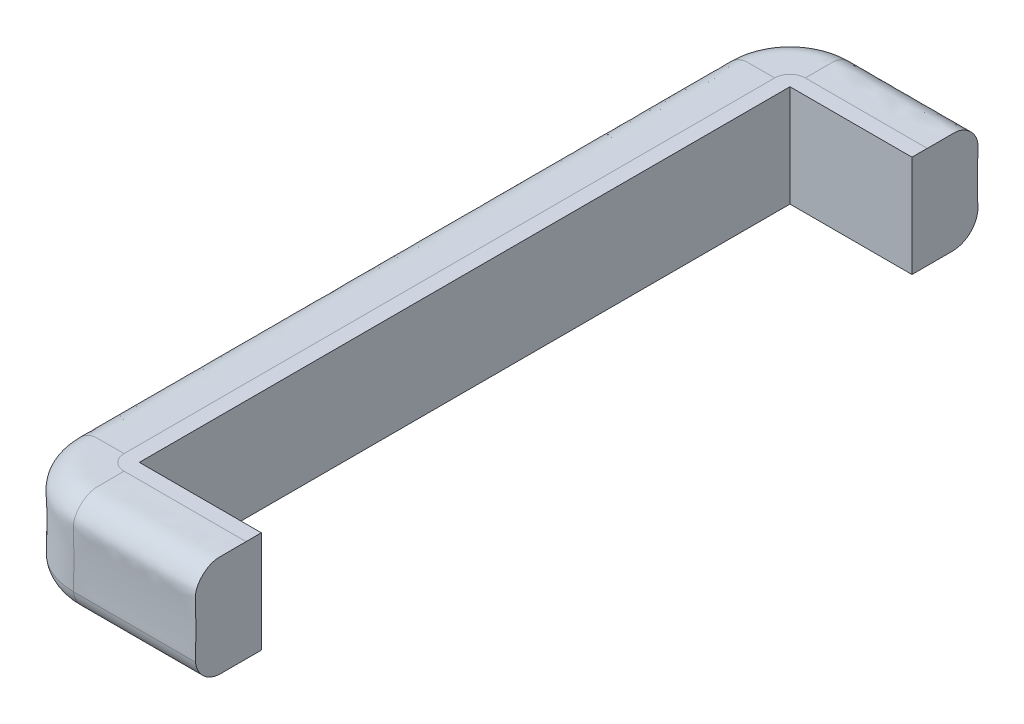
SolidWorks part; units mm, degrees
material "Polyurethane Foam Flexible"
ref_plane "Front Plane" through (0, 0, 0) normal (0, 0, 1) x (1, 0, 0)
ref_plane "Top Plane" through (0, 0, 0) normal (0, 1, 0) x (1, 0, 0)
ref_plane "Right Plane" through (0, 0, 0) normal (1, 0, 0) x (0, 0, -1)
sketch "Sketch1" plane through (0, 0, 0) normal (0, 0, 1) x (1, 0, 0)
  line L0 (-42.938, 0) -> (-64.5194, 0) construction
  line L1 (0, 0) -> (-19.05, 0)
  line L2 (0, 0) -> (0, 127)
  line L3 (0, 127) -> (-19.05, 127)
  line L4 (-19.05, 0) -> (-19.05, 127)
  line L5 (-82.4248, 61.7932) -> (-82.5169, 106.4686) construction
  line L6 (-82.3392, 20.316) -> (-82.421, 59.9925) construction
  line L7 (-25.1859, 127) -> (-9.5237, 127) construction
  line L8 (-59.4349, 127) -> (-40.1051, 127) construction
  circle A0 centre (-50.8, 95.25) radius 31.75
  circle A1 centre (-50.8, 31.75) radius 31.75
  spline S0 degree 3 poles (-19.05, 127) (-25.8552, 127) (-41.6978, 126.7791) (-65.8751, 127.402) (-83.5455, 110.8616) (-81.483, 80.6655) (-81.4888, 44.9734) (-83.2203, 14.9745) (-68.5084, -0.3764) (-39.2535, 0.2129) (-30.1777, 0.1792) (-19.05, 0) knots 0 0 0 0 0.126865 0.164018 0.34847 0.398266 0.612182 0.660911 0.836821 0.872929 1 1 1 1
  dimension "D1" = 19.05
  dimension "D2" = 63.5
extrude "Boss-Extrude1" add sketch "Sketch1" along normal blind 812.8 contours A0 S0 A1 | A1 L4 A0 | L4 S0 A0 | A0 S0 | A1 S0 | A0 S0 | A1 S0 L4 | L4 L1 L2 L3
sketch "Sketch2" plane through (0, 0, 812.8) normal (0, 0, 1) x (1, 0, 0)
  line L3 (-19.05, 0) -> (0, 0)
  line L4 (0, 0) -> (0, 127)
  line L5 (0, 127) -> (-19.05, 127)
  line L6 (-19.05, 0) -> (0, 0)
  line L7 (0, 0) -> (0, 127)
  line L8 (0, 127) -> (-19.05, 127)
  arc A1 (-82.3555, 28.2414) -> (-50.8, 0) centre (-50.8, 31.75) ccw
  arc A2 (-82.3555, 28.2414) -> (-50.8, 0) centre (-50.8, 31.75) ccw
  spline S2 degree 3 poles (-3014.4787, -37.5012) (256.1734, 142.9451) (16.9783, 125.2675) (-65.8751, 127.402) (-83.5455, 110.8616) (-81.483, 80.6655) (-81.5023, -38.9836) (-96.4116, 20.7178) (2684.799, -1129.6695) knots -0.845708 -0.845708 -0.845708 -0.845708 0.126865 0.164018 0.34847 0.398266 0.612182 1.39585 1.39585 1.39585 1.39585 only from (-19.05, 127) to (-82.3555, 28.2414)
  spline S3 degree 3 poles (1998.3135, 2187.1841) (-227.7169, -6.5891) (99.7338, 8.0795) (-73.8503, -9.0254) (2980.7785, -12.4885) knots 0.228756 0.228756 0.228756 0.228756 0.872929 1.861828 1.861828 1.861828 1.861828 only from (-50.8, 0) to (-19.05, 0)
  spline S4 degree 3 poles (-19.05, 127) (-25.8552, 127) (-41.6978, 126.7791) (-65.8751, 127.402) (-83.5455, 110.8616) (-81.483, 80.6655) (-81.4884, 47.4854) (-82.3594, 30.1001) (-82.3555, 28.2414) knots 0 0 0 0 0.126865 0.164018 0.34847 0.398266 0.612182 0.638922 0.638922 0.638922 0.638922
  spline S5 degree 3 poles (-50.8, 0) (-49.6284, 0) (-38.0305, 0.2084) (-30.1777, 0.1792) (-19.05, 0) knots 0.85881 0.85881 0.85881 0.85881 0.872929 1 1 1 1
  dimension "D1" = 0
revolve "Revolve1" add sketch "Sketch2" angle 90 about L7
sketch "Sketch4" plane through (0, 0, 0) normal (0, 0, -1) x (-1, 0, 0)
  line L3 (19.05, 127) -> (0, 127)
  line L4 (0, 127) -> (0, 0)
  line L5 (0, 0) -> (19.05, 0)
  line L6 (19.05, 127) -> (0, 127)
  line L7 (0, 127) -> (0, 0)
  line L8 (0, 0) -> (19.05, 0)
  arc A1 (50.8, 0) -> (82.3555, 28.2414) centre (50.8, 31.75) ccw
  arc A2 (50.8, 0) -> (82.3555, 28.2414) centre (50.8, 31.75) ccw
  spline S2 degree 3 poles (-2684.8304, -1129.6825) (96.4117, 20.7181) (81.5023, -38.9839) (81.483, 80.6655) (83.5455, 110.8616) (65.8751, 127.402) (-16.9777, 125.2675) (-256.1693, 142.9448) (3014.3918, -37.4964) knots -0.756931 -0.756931 -0.756931 -0.756931 0.026739 0.240655 0.290451 0.474904 0.512057 1.484621 1.484621 1.484621 1.484621 only from (82.3555, 28.2414) to (19.05, 127)
  spline S3 degree 3 poles (-2980.8609, -12.4886) (73.8522, -9.0256) (-99.7352, 8.0795) (227.7155, -6.5891) (-1998.2775, 2187.1486) knots -0.003027 -0.003027 -0.003027 -0.003027 0.985881 1.630051 1.630051 1.630051 1.630051 only from (19.05, 0) to (50.8, 0)
  spline S4 degree 3 poles (82.3555, 28.2414) (82.3594, 30.1001) (81.4884, 47.4854) (81.483, 80.6655) (83.5455, 110.8616) (65.8751, 127.402) (41.6978, 126.7791) (25.8552, 127) (19.05, 127) knots 0 0 0 0 0.026739 0.240655 0.290451 0.474904 0.512057 0.638922 0.638922 0.638922 0.638922
  spline S5 degree 3 poles (19.05, 0) (30.1777, 0.1792) (38.0305, 0.2084) (49.6284, 0) (50.8, 0) knots 0.85881 0.85881 0.85881 0.85881 0.985881 1 1 1 1
  dimension "D1" = 0
revolve "Revolve2" add sketch "Sketch4" angle 90 about L7
sketch "Sketch5" plane through (0, 0, 0) normal (1, 0, 0) x (0, 0, -1)
  line L0 (-812.8, 127) -> (-812.8, 0)
  line L1 (-812.8, 127) -> (-812.8, 28.2414) construction
  line L2 (-831.85, 0) -> (19.05, 0)
  line L3 (19.05, 127) -> (-831.85, 127)
  line L4 (-831.85, 0) -> (19.05, 0)
  line L5 (19.05, 127) -> (-831.85, 127)
  line L6 (0, 127) -> (0, 0)
  arc A2 (50.8, 0) -> (82.3555, 28.2414) centre (50.8, 31.75) ccw
  arc A3 (-895.1555, 28.2414) -> (-863.6, 0) centre (-863.6, 31.75) ccw
  arc A4 (50.8, 0) -> (82.3555, 28.2414) centre (50.8, 31.75) ccw
  arc A5 (-895.1555, 28.2414) -> (-863.6, 0) centre (-863.6, 31.75) ccw
  spline S4 degree 3 poles (-2980.8609, -12.4886) (73.8522, -9.0256) (-99.7352, 8.0795) (227.7155, -6.5891) (-1998.2775, 2187.1486) knots -0.003027 -0.003027 -0.003027 -0.003027 0.985881 1.630051 1.630051 1.630051 1.630051 only from (19.05, 0) to (50.8, 0)
  spline S5 degree 3 poles (-2684.8304, -1129.6825) (96.4117, 20.7181) (81.5023, -38.9839) (81.483, 80.6655) (83.5455, 110.8616) (65.8751, 127.402) (-16.9777, 125.2675) (-256.1693, 142.9448) (3014.3918, -37.4964) knots -0.756931 -0.756931 -0.756931 -0.756931 0.026739 0.240655 0.290451 0.474904 0.512057 1.484621 1.484621 1.484621 1.484621 only from (82.3555, 28.2414) to (19.05, 127)
  spline S6 degree 3 poles (-3827.2787, -37.5012) (-556.6266, 142.9451) (-795.8217, 125.2675) (-878.6751, 127.402) (-896.3455, 110.8616) (-894.283, 80.6655) (-894.3023, -38.9836) (-909.2116, 20.7178) (1871.999, -1129.6695) knots -0.845708 -0.845708 -0.845708 -0.845708 0.126865 0.164018 0.34847 0.398266 0.612182 1.39585 1.39585 1.39585 1.39585 only from (-831.85, 127) to (-895.1555, 28.2414)
  spline S7 degree 3 poles (1185.5135, 2187.1841) (-1040.5169, -6.5891) (-713.0662, 8.0795) (-886.6503, -9.0254) (2167.9785, -12.4885) knots 0.228756 0.228756 0.228756 0.228756 0.872929 1.861828 1.861828 1.861828 1.861828 only from (-863.6, 0) to (-831.85, 0)
  spline S8 degree 3 poles (19.05, 0) (30.1777, 0.1792) (38.0305, 0.2084) (49.6284, 0) (50.8, 0) knots 0.85881 0.85881 0.85881 0.85881 0.985881 1 1 1 1
  spline S9 degree 3 poles (82.3555, 28.2414) (82.3594, 30.1001) (81.4884, 47.4854) (81.483, 80.6655) (83.5455, 110.8616) (65.8751, 127.402) (41.6978, 126.7791) (25.8552, 127) (19.05, 127) knots 0 0 0 0 0.026739 0.240655 0.290451 0.474904 0.512057 0.638922 0.638922 0.638922 0.638922
  spline S10 degree 3 poles (-831.85, 127) (-838.6552, 127) (-854.4978, 126.7791) (-878.6751, 127.402) (-896.3455, 110.8616) (-894.283, 80.6655) (-894.2884, 47.4854) (-895.1594, 30.1001) (-895.1555, 28.2414) knots 0 0 0 0 0.126865 0.164018 0.34847 0.398266 0.612182 0.638922 0.638922 0.638922 0.638922
  spline S11 degree 3 poles (-863.6, 0) (-862.4284, 0) (-850.8305, 0.2084) (-842.9777, 0.1792) (-831.85, 0) knots 0.85881 0.85881 0.85881 0.85881 0.872929 1 1 1 1
  line M10 (-831.85, 0) -> (19.05, 0)
  spline M11 degree 3 poles (19.05, 0) (30.1777, 0.1792) (38.0305, 0.2084) (49.6284, 0) (50.8, 0) knots 0.85881 0.85881 0.85881 0.85881 0.985881 1 1 1 1
  arc M12 (50.8, 0) -> (82.3555, 28.2414) centre (50.8, 31.75) ccw
  spline M13 degree 3 poles (82.3555, 28.2414) (82.3594, 30.1001) (81.4884, 47.4854) (81.483, 80.6655) (83.5455, 110.8616) (65.8751, 127.402) (41.6978, 126.7791) (25.8552, 127) (19.05, 127) knots 0 0 0 0 0.026739 0.240655 0.290451 0.474904 0.512057 0.638922 0.638922 0.638922 0.638922
  line M14 (19.05, 127) -> (-831.85, 127)
  spline M15 degree 3 poles (-831.85, 127) (-838.6552, 127) (-854.4978, 126.7791) (-878.6751, 127.402) (-896.3455, 110.8616) (-894.283, 80.6655) (-894.2884, 47.4854) (-895.1594, 30.1001) (-895.1555, 28.2414) knots 0 0 0 0 0.126865 0.164018 0.34847 0.398266 0.612182 0.638922 0.638922 0.638922 0.638922
  arc M16 (-895.1555, 28.2414) -> (-863.6, 0) centre (-863.6, 31.75) ccw
  spline M17 degree 3 poles (-863.6, 0) (-862.4284, 0) (-850.8305, 0.2084) (-842.9777, 0.1792) (-831.85, 0) knots 0.85881 0.85881 0.85881 0.85881 0.872929 1 1 1 1
  dimension "D1" = 0
extrude "Boss-Extrude2" add sketch "Sketch5" along normal blind 152.4 contours L0 M14 M15 M16 M17 M10 | L6 L4 M14 M11 M12 M13
equation "\"Thick\"= \"in\""
